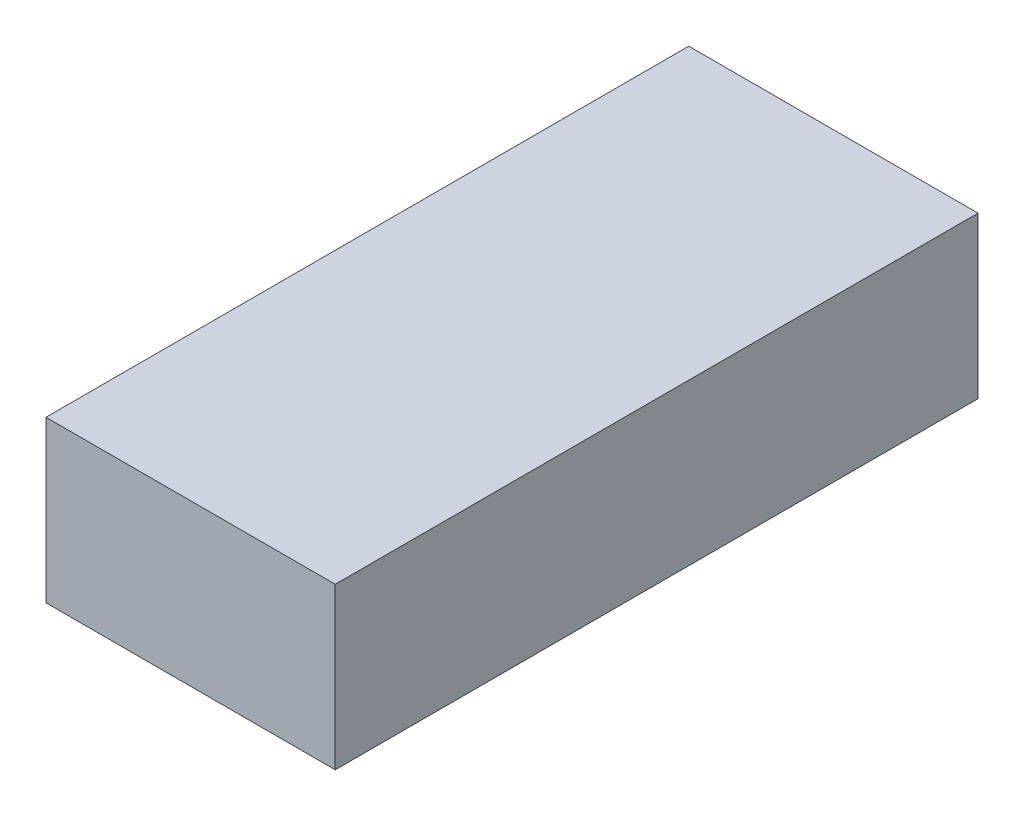
SolidWorks part; units mm, degrees
ref_plane "Front Plane" through (0, 0, 0) normal (0, 0, 1) x (1, 0, 0)
ref_plane "Top Plane" through (0, 0, 0) normal (0, 1, 0) x (1, 0, 0)
ref_plane "Right Plane" through (0, 0, 0) normal (1, 0, 0) x (0, 0, -1)
sketch "Sketch1" plane through (0, 0, 0) normal (0, 1, 0) x (1, 0, 0)
  line L1 (0, 0) -> (4.5, 0)
  line L2 (0, 0) -> (0, 10)
  line L3 (0, 10) -> (4.5, 10)
  line L4 (4.5, 0) -> (4.5, 10)
  dimension "D1" = 10
  dimension "D2" = 4.5
extrude "Boss-Extrude1" add sketch "Sketch1" along normal blind 2.5 contours L4 L3 L2 L1
sketch "Sketch2" plane through (0, 0, 0) normal (-1, 0, 0) x (0, 0, 1)
  line L0 (-10, 1.25) -> (0, 1.25) construction
  line L1 (-10, 2.5) -> (-10, 0) construction
  line L2 (0, 2.5) -> (0, 0) construction
  line L3 (-5, 0) -> (-5, 2.5) construction
  line L4 (0, 0) -> (-10, 0) construction
  line L5 (0, 2.5) -> (-10, 2.5) construction
  circle A0 centre (-9.35, 1.25) radius 0.5
  dimension "D1" = 1
  dimension "D2" = 0.65
